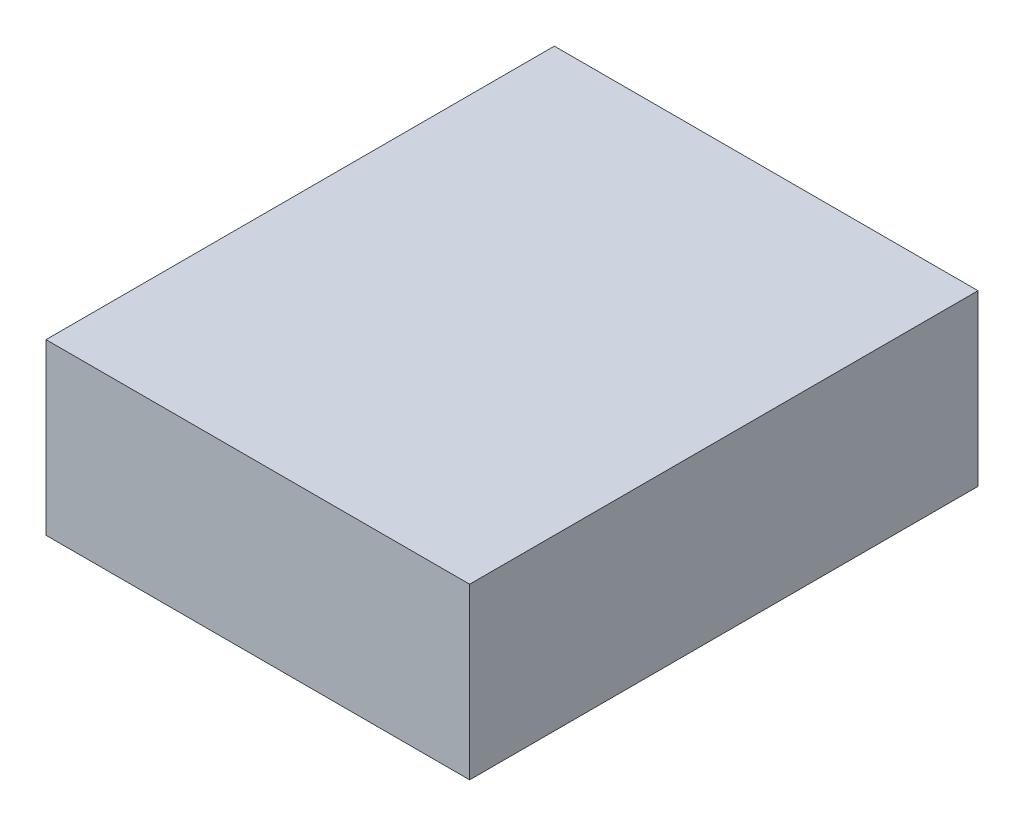
SolidWorks part; units mm, degrees
ref_plane "Front Plane" through (0, 0, 0) normal (0, 0, 1) x (1, 0, 0)
ref_plane "Top Plane" through (0, 0, 0) normal (0, 1, 0) x (1, 0, 0)
ref_plane "Right Plane" through (0, 0, 0) normal (1, 0, 0) x (0, 0, -1)
sketch "Sketch1" plane through (0, 0, 0) normal (0, 1, 0) x (1, 0, 0)
  line L1 (2.5, -3) -> (-2.5, -3)
  line L2 (2.5, -3) -> (2.5, 3)
  line L3 (2.5, 3) -> (-2.5, 3)
  line L4 (-2.5, -3) -> (-2.5, 3)
  line L5 (2.5, -3) -> (-2.5, 3) construction
  line L6 (2.5, 3) -> (-2.5, -3) construction
  point P0 (0, 0)
  dimension "D1" = 5
  dimension "D2" = 6
extrude "Boss-Extrude1" add sketch "Sketch1" along normal blind 2
